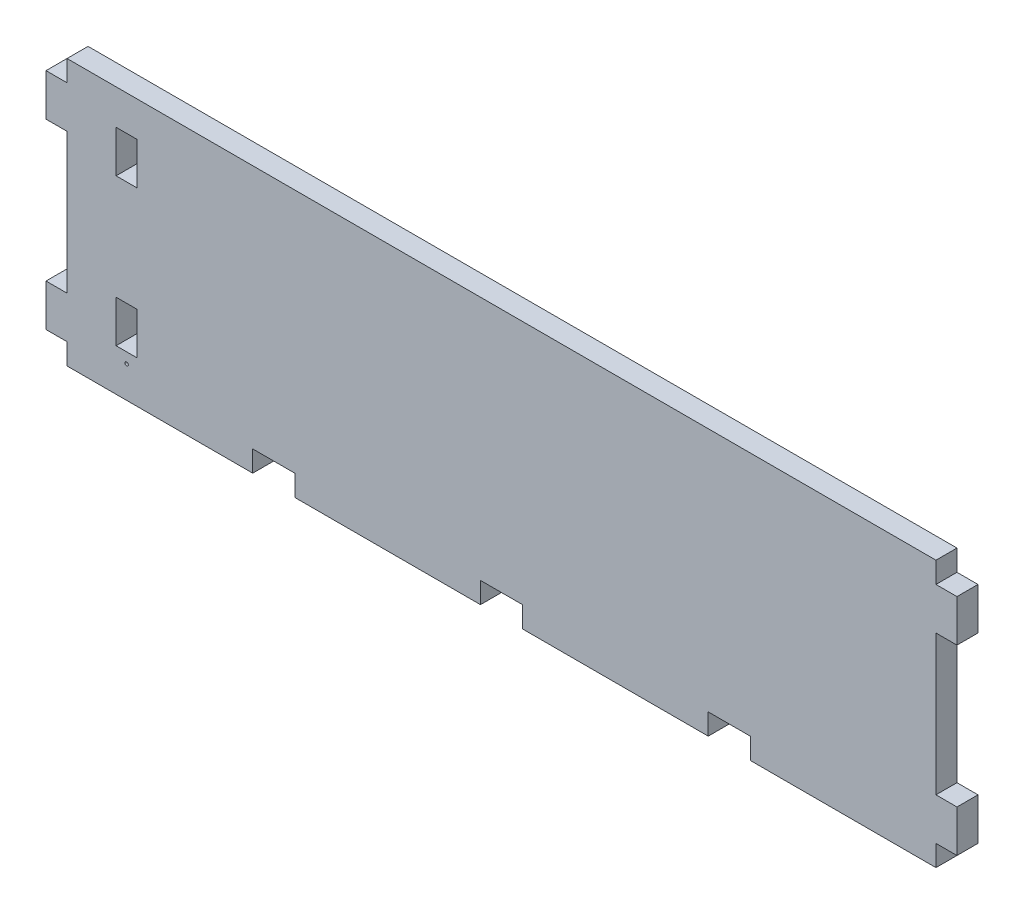
SolidWorks part; units mm, degrees
ref_plane "Front Plane" through (0, 0, 0) normal (0, 0, 1) x (1, 0, 0)
ref_plane "Top Plane" through (0, 0, 0) normal (0, 1, 0) x (1, 0, 0)
ref_plane "Right Plane" through (0, 0, 0) normal (1, 0, 0) x (0, 0, -1)
sketch "Sketch2" plane through (0, 0, 0) normal (0, 1, 0) x (1, 0, 0)
  line L0 (0, 0) -> (0, 6) construction
  dimension "D1" = 6
sketch "Sketch1" plane through (0, 0, 0) normal (0, 0, 1) x (1, 0, 0)
  line L0 (-124, 32) -> (-124, 38)
  line L1 (-130, -38) -> (130, -38)
  line L2 (-130, -38) -> (-130, 38)
  line L3 (-130, 38) -> (130, 38)
  line L4 (130, -38) -> (130, 38)
  line L5 (-130, -38) -> (130, 38) construction
  line L6 (-130, 38) -> (130, -38) construction
  line L7 (-130, -32) -> (-124, -32)
  line L8 (-130, -32) -> (-130, -20)
  line L9 (-130, -20) -> (-124, -20)
  line L10 (-124, -32) -> (-124, -20)
  line L11 (-130, 32) -> (-124, 32)
  line L12 (-130, 32) -> (-130, 20)
  line L13 (-130, 20) -> (-124, 20)
  line L14 (-124, 32) -> (-124, 20)
  line L15 (130, 32) -> (124, 32)
  line L16 (130, 32) -> (130, 20)
  line L17 (130, 20) -> (124, 20)
  line L18 (124, 32) -> (124, 20)
  line L19 (124, -20) -> (130, -20)
  line L20 (124, -20) -> (124, -32)
  line L21 (124, -32) -> (130, -32)
  line L22 (130, -20) -> (130, -32)
  line L23 (-124, -32) -> (-124, -38)
  line L24 (-124, 20) -> (-124, -20)
  line L25 (124, 32) -> (124, 38)
  line L26 (124, 20) -> (124, -20)
  line L27 (124, -32) -> (124, -38)
  line L28 (-124, 0) -> (-110, 0) construction
  line L29 (71, -32) -> (124, -32) construction
  line L30 (-110, 0) -> (-110, 16) construction
  line L31 (-110, 16) -> (-110, 28)
  line L32 (-110, 28) -> (-110, 38) construction
  line L33 (-110, 28) -> (-104, 28)
  line L34 (-104, 28) -> (-104, 16)
  line L35 (-104, 16) -> (-110, 16)
  line L36 (-110, -26) -> (-110, -14)
  line L37 (-110, -14) -> (-104, -14)
  line L38 (-104, -14) -> (-104, -26)
  line L39 (-104, -26) -> (-110, -26)
  line L40 (-110, -32) -> (-110, -26) construction
  line L41 (-110, -14) -> (-110, 0) construction
  line L42 (-124, -32) -> (-71, -32) construction
  line L43 (6, -38) -> (-6, -38)
  line L44 (6, -38) -> (6, -32)
  line L45 (6, -32) -> (-6, -32)
  line L46 (-6, -38) -> (-6, -32)
  line L47 (59, -38) -> (71, -38)
  line L48 (59, -38) -> (59, -32)
  line L49 (59, -32) -> (71, -32)
  line L50 (71, -38) -> (71, -32)
  line L51 (-59, -38) -> (-71, -38)
  line L52 (-59, -38) -> (-59, -32)
  line L53 (-59, -32) -> (-71, -32)
  line L54 (-71, -38) -> (-71, -32)
  line L55 (-59, -32) -> (-6, -32) construction
  line L56 (6, -32) -> (59, -32) construction
  point P0 (0, 0)
  dimension "D1" = 260
  dimension "D2" = 76
  dimension "D3" = 6
  dimension "D4" = 12
  dimension "D5" = 14
  dimension "D6" = 10
extrude "Boss-Extrude1" add sketch "Sketch1" against normal up to vertex (6 mm away) contours L1 L54 L53 L52 L46 L45 L44 L48 L49 L50 L27 L20 L26 L18 L25 L3 L0 L14 L24 L10 L23 L34 L35 L31 L33 L38 L39 L36 L37 | L7 L10 L9 L2 | L14 L11 L2 L13 | L15 L18 L17 L4 | L20 L21 L4 L19 up to point (0, 0, -6)
sketch "Sketch3" plane through (0, 0, 0) normal (0, 0, 1) x (1, 0, 0)
  line L0 (-107, -26) -> (-107, -29) construction
  line L1 (-104, -26) -> (-110, -26) construction
  line L2 (-124, -38) -> (-71, -38) construction
  circle A0 centre (-107, -29) radius 0.5
  dimension "D2" = 1
  dimension "D1" = 9
extrude "Cut-Extrude1" cut sketch "Sketch3" against normal through all
equation "\"t_wood\"= 6' Thickness of the wood"
equation "\"t_glass\"= 2.5'Thickness of glass panels"
equation "\"w_glass\"= 248"
equation "\"h_glass\"= 167"
equation "\"h_food_internal\" = 60"
equation "\"entry_height\"= 20"
equation "\"entry diameter\"= 8"
equation "\"glass_bottom_overlap\"= 8"
equation "\"default_finger_size\"= 12"
equation "\"brood_depth\"= 42"
equation "\"outer_box_depth\" = \"brood_depth\" + ( 2 * \"t_glass\" ) + ( 2 * \"t_wood\" )"
equation "\"outer_box_width\"= \"w_glass\" + ( 2 * \"t_wood\" )"
equation "\"food_top_clearance\"= 10"
equation "\"outer_box_height\"= \"t_wood\" + \"h_glass\" + \"t_wood\" + \"h_food_internal\" + \"food_top_clearance\" + \"t_wood\""
equation "\"food_internal_depth\"= \"brood_depth\" + \"t_glass\" + \"t_glass\" - \"t_wood\" - \"t_wood\""
equation "\"food_channel_clearance_width\"= 14"
equation "\"bar_top_play\"= 4.5"
equation "\"bar_entry_angle\"= 10"
equation "\"bar_width\"= 20"
equation "\"entry_disk_play\"= 0.3"
equation "\"D1@Sketch2\"=\"t_wood\""
equation "\"D1@Sketch1\"=\"outer_box_width\""
equation "\"D2@Sketch1\"=\"h_food_internal\"+\"t_wood\"+\"food_top_clearance\""
equation "\"D3@Sketch1\"=\"t_wood\""
equation "\"D4@Sketch1\"=\"default_finger_size\""
equation "\"D5@Sketch1\"=\"food_channel_clearance_width\""
equation "\"D6@Sketch1\"=\"food_top_clearance\""
